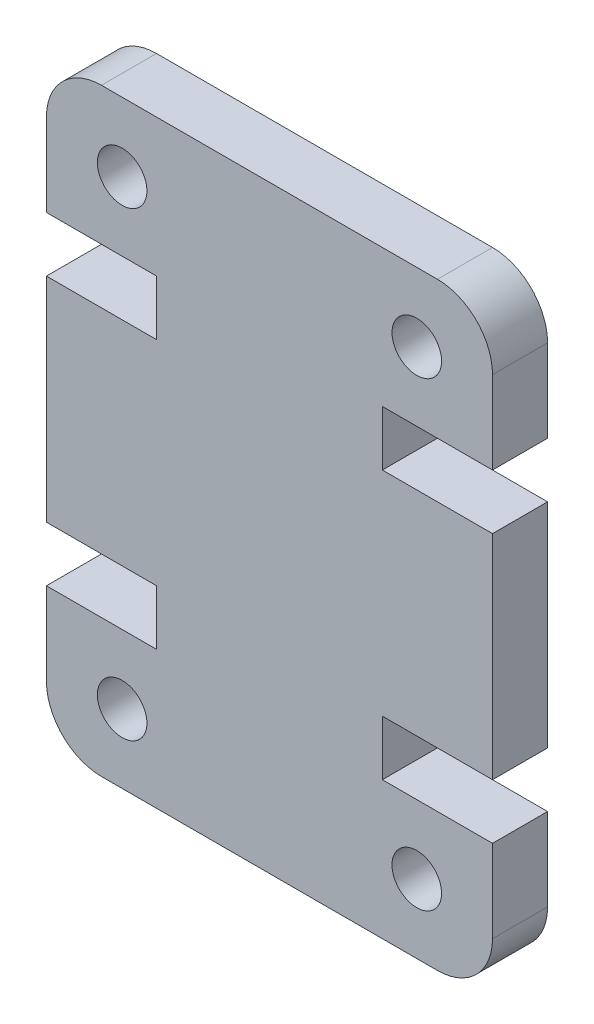
SolidWorks part; units mm, degrees
ref_plane "Front Plane" through (0, 0, 0) normal (0, 0, 1) x (1, 0, 0)
ref_plane "Top Plane" through (0, 0, 0) normal (0, 1, 0) x (1, 0, 0)
ref_plane "Right Plane" through (0, 0, 0) normal (1, 0, 0) x (0, 0, -1)
sketch "Sketch1" plane through (0, 0, 0) normal (0, 0, 1) x (1, 0, 0)
  line L0 (0, 14.74) -> (0, 7)
  line L1 (16.2, 2) -> (16.2, 5)
  line L2 (12.2, 5) -> (16.2, 5)
  line L3 (2, 0) -> (14.2, 0)
  line L4 (16.2, 7) -> (12.2, 7)
  line L5 (12.2, 7) -> (12.2, 5)
  line L6 (16.2, 14.74) -> (16.2, 7)
  line L7 (4, 7) -> (4, 5)
  line L8 (0, 19.74) -> (0, 16.74)
  line L9 (4, 16.74) -> (0, 16.74)
  line L10 (0, 7) -> (4, 7)
  line L11 (0, 14.74) -> (4, 14.74)
  line L12 (4, 5) -> (0, 5)
  line L13 (4, 14.74) -> (4, 16.74)
  line L14 (12.2, 14.74) -> (12.2, 16.74)
  line L15 (16.2, 14.74) -> (12.2, 14.74)
  line L16 (0, 2) -> (0, 5)
  line L17 (2, 21.74) -> (14.2, 21.74)
  line L18 (12.2, 16.74) -> (16.2, 16.74)
  line L19 (16.2, 19.74) -> (16.2, 16.74)
  line L20 (8.1, 21.74) -> (8.1, 0) construction
  line L21 (0, 10.87) -> (16.2, 10.87) construction
  circle A0 centre (13.45, 2.5) radius 0.9
  arc A1 (16.2, 2) -> (14.2, 0) centre (14.2, 2) cw
  circle A2 centre (2.75, 19.24) radius 0.9
  arc A3 (0, 2) -> (2, 0) centre (2, 2) ccw
  arc A4 (0, 19.74) -> (2, 21.74) centre (2, 19.74) cw
  circle A5 centre (2.75, 2.5) radius 0.9
  arc A6 (16.2, 19.74) -> (14.2, 21.74) centre (14.2, 19.74) ccw
  circle A7 centre (13.45, 19.24) radius 0.9
  point P15 (8.1, 10.87)
  dimension "D1" = 1.8
  dimension "D2" = 2
  dimension "D3" = 2.75
  dimension "D4" = 8.1
  dimension "D5" = 2.5
  dimension "D6" = 5
  dimension "D8" = 10.87
extrude "Boss-Extrude1" add sketch "Sketch1" along normal blind 4
sketch "Sketch2" plane through (0, 0, 0) normal (0, 0, -1) x (-1, 0, 0)
  line L0 (0, 0) -> (-16.2, 0)
  line L1 (-16.2, 0) -> (-16.2, 21.74)
  line L2 (-16.2, 21.74) -> (0, 21.74)
  line L3 (0, 21.74) -> (0, 0)
extrude "Cut-Extrude1" cut sketch "Sketch2" against normal blind 2
equation "\"D4@Sketch1\"= \"fingerWidth@parametersSketch@prostheticParameters.SLDPRT\" / 2'PIP width"
equation "\"D8@Sketch1\"= ( \"HL@parametersSketch@prostheticParameters.SLDPRT\" * 0.204 - 4 - 12 ) / 2 'PIP length - Sil. Sht MIP - Sil.Sht PIP"
equation "\"D1@Sketch1\"= 1.5 + \"tol1@parametersSketch@prostheticParameters.SLDPRT\""
